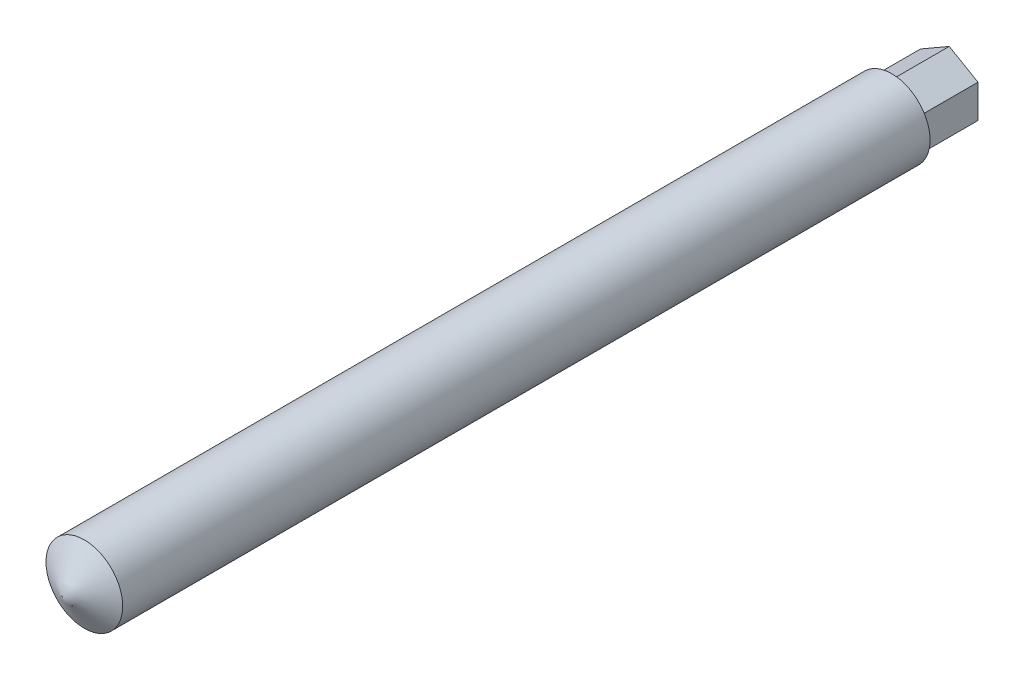
SolidWorks part; units mm, degrees
material "AISI 1020"
ref_plane "Спереди" through (0, 0, 0) normal (0, 0, 1) x (1, 0, 0)
ref_plane "Сверху" through (0, 0, 0) normal (0, 1, 0) x (1, 0, 0)
ref_plane "Справа" through (0, 0, 0) normal (1, 0, 0) x (0, 0, -1)
sketch "Эскиз1" plane through (0, 0, 0) normal (1, 0, 0) x (0, 0, -1)
  line L0 (-756.5808, 0) -> (37072.4593, 0) construction
  line L1 (-176.3509, 0) -> (40, 0)
  line L2 (40, 0) -> (40, 10)
  line L3 (40, 10) -> (-170.5774, 10)
  line L4 (-170.5774, 10) -> (-176.3509, 0)
  line L5 (-170, 11) -> (-176.3509, 0) construction
  line L6 (0, -18) -> (0, 18) construction
  dimension "D1" = 20
  dimension "D2" = 40
revolve "Повернуть1" add sketch "Эскиз1" angle 360 about L0
cosmetic thread "Условное изображение резьбы1" parameters "D2"=17.797
sketch "Эскиз4" plane through (0, 0, -40) normal (0, 0, -1) x (-1, 0, 0)
  line L1 (0, 8.6603) -> (-7.5, 4.3301)
  line L2 (-7.5, 4.3301) -> (-7.5, -4.3301)
  line L3 (-7.5, -4.3301) -> (0, -8.6603)
  line L4 (0, -8.6603) -> (7.5, -4.3301)
  line L5 (7.5, -4.3301) -> (7.5, 4.3301)
  line L6 (7.5, 4.3301) -> (0, 8.6603)
  circle A0 centre (0, 0) radius 7.5 construction
  dimension "D1" = 15
extrude "Бобышка-Вытянуть1" add sketch "Эскиз4" along normal blind 15
